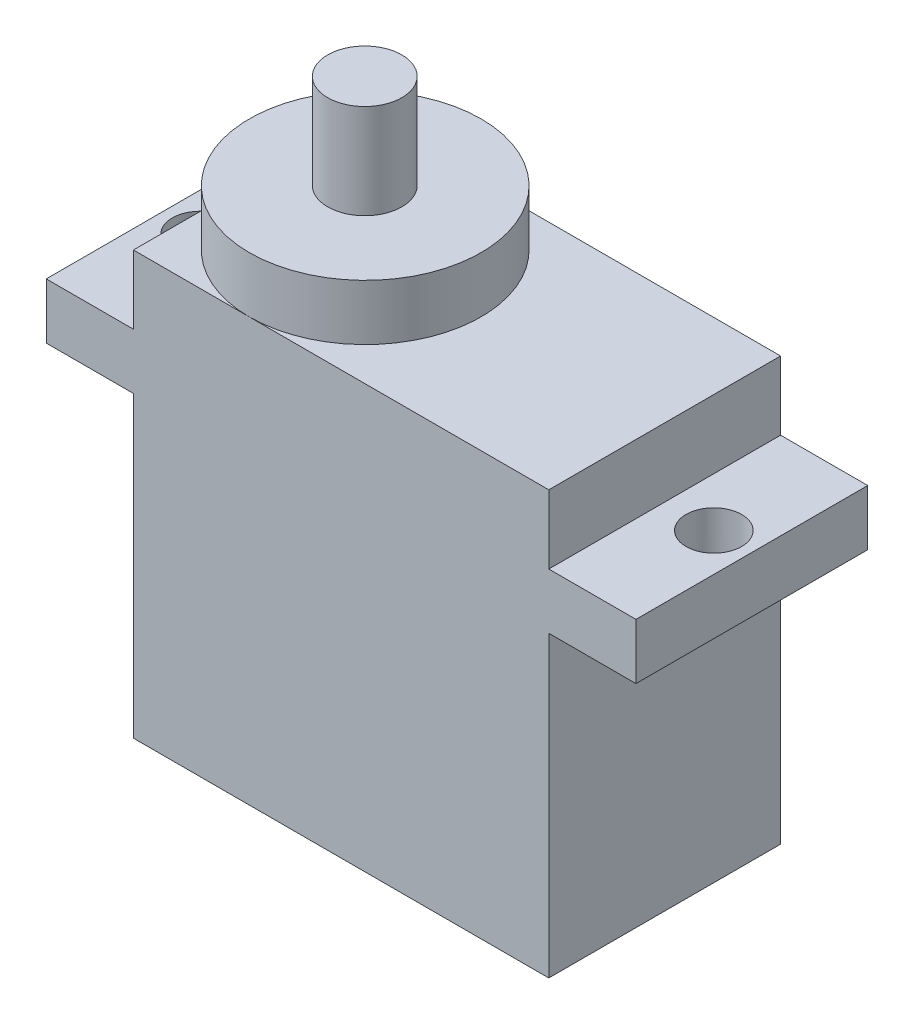
SolidWorks part; units mm, degrees
ref_plane "前视基准面" through (0, 0, 0) normal (0, 0, 1) x (1, 0, 0)
ref_plane "上视基准面" through (0, 0, 0) normal (0, 1, 0) x (1, 0, 0)
ref_plane "右视基准面" through (0, 0, 0) normal (1, 0, 0) x (0, 0, -1)
sketch "草图1" plane through (0, 0, 0) normal (0, 1, 0) x (1, 0, 0)
  line L3 (0, -12.5) -> (0, 0)
  line L4 (0, -12.5) -> (22.4, -12.5)
  line L5 (22.4, -12.5) -> (22.4, 0)
  line L7 (22.4, 0) -> (0, 0)
  point P3 (218.1429, -3.8419)
extrude "凸台-拉伸1" add sketch "草图1" along normal blind 22.8 contours L5 L7 L3 L4
sketch "草图2" plane through (22.4, 0, 0) normal (1, 0, 0) x (0, 0, -1)
  line L0 (-12.5, 19.1) -> (0, 19.1)
  line L1 (-12.5, 22.8) -> (-12.5, 0) construction
  line L2 (0, 22.8) -> (0, 0) construction
  line L3 (0, 19.1) -> (0, 16.1)
  line L4 (0, 16.1) -> (-12.5, 16.1)
  line L5 (-12.5, 16.1) -> (-12.5, 19.1)
  line L6 (-12.5, 0) -> (0, 0) construction
  dimension "D1" = 16.1
extrude "凸台-拉伸2" add sketch "草图2" along normal blind 4.7 contours L5 L0 L3 L4
sketch "草图3" plane through (0, 0, 0) normal (-1, 0, 0) x (0, 0, 1)
  line L0 (0, 19.1) -> (12.5, 19.1)
  line L1 (0, 22.8) -> (0, 0) construction
  line L2 (12.5, 22.8) -> (12.5, 0) construction
  line L3 (12.5, 19.1) -> (12.5, 16.1)
  line L4 (12.5, 16.1) -> (0, 16.1)
  line L5 (0, 16.1) -> (0, 19.1)
  line L6 (12.5, 0) -> (0, 0) construction
  dimension "D1" = 16.1
extrude "凸台-拉伸3" add sketch "草图3" along normal blind 4.7 contours L5 L0 L3 L4
sketch "草图4" plane through (0, 19.1, 0) normal (0, 1, 0) x (1, 0, 0)
  line L0 (0, 0) -> (0, -12.5) construction
  line L7 (-4.7711, -6.25) -> (-6.8391, -6.25) construction
  line L9 (-4.7, 0) -> (-4.7, -12.5) construction
  line L10 (22.4, -12.5) -> (22.4, 0) construction
  circle A0 centre (-2.65, -6.25) radius 1.5
  circle A1 centre (25.05, -6.25) radius 1.5
  point P9 (-4.7, -6.25)
  point P12 (0, 0)
  dimension "D2" = 2.65
  dimension "D1" = 2.65
extrude "切除-拉伸1" cut sketch "草图4" against normal blind 4.7
sketch "草图5" plane through (0, 22.8, 0) normal (0, 1, 0) x (1, 0, 0)
  line L0 (0.6769, -6.25) -> (7.9897, -6.25) construction
  line L2 (0, -12.5) -> (0, 0) construction
  circle A0 centre (6.25, -6.25) radius 6.25
extrude "凸台-拉伸5" add sketch "草图5" along normal blind 3
sketch "草图6" plane through (0, 25.8, 0) normal (0, 1, 0) x (1, 0, 0)
  line L0 (0, -6.25) -> (7.5847, -6.25) construction
  line L2 (6.25, -12.5) -> (6.25, -6.25) construction
  circle A0 centre (6.2255, -6.25) radius 2
extrude "凸台-拉伸6" add sketch "草图6" along normal blind 5.1
